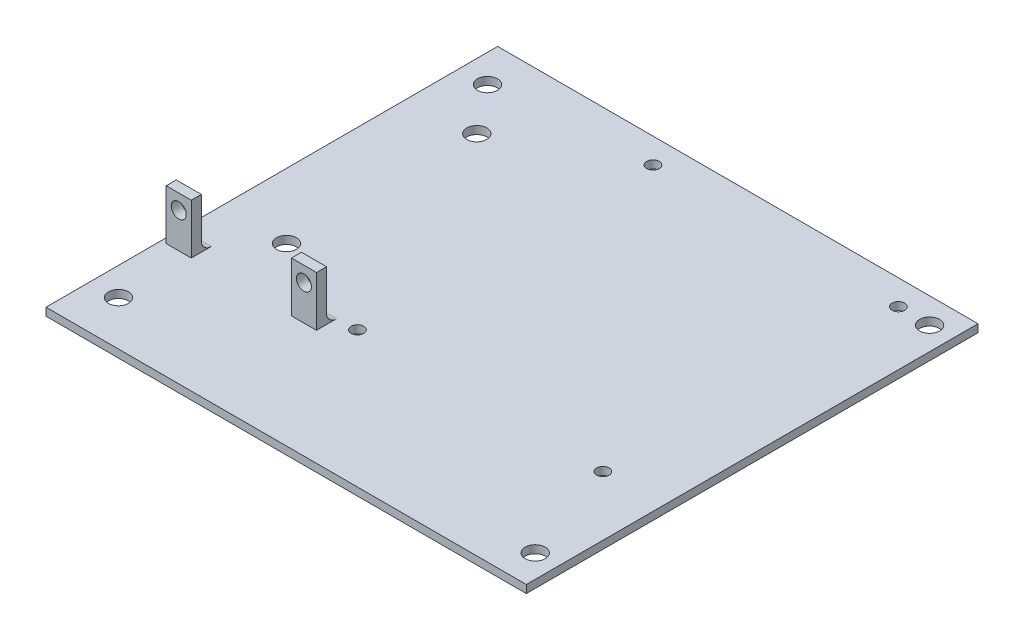
SolidWorks part; units mm, degrees
other "DetailItem3"
material "ABS"
ref_plane "Front Plane" through (0, 0, 0) normal (0, 0, 1) x (1, 0, 0)
ref_plane "Top Plane" through (0, 0, 0) normal (0, 1, 0) x (1, 0, 0)
ref_plane "Right Plane" through (0, 0, 0) normal (1, 0, 0) x (0, 0, -1)
sketch "Sketch1" plane through (0, 0, 0) normal (0, 1, 0) x (1, 0, 0)
  line L1 (-32.2441, 108.719) -> (64.6459, 108.719)
  line L2 (-32.2441, 108.719) -> (-32.2441, 18.549)
  line L3 (-32.2441, 18.549) -> (64.6459, 18.549)
  line L4 (64.6459, 108.719) -> (64.6459, 18.549)
  dimension "D1" = 96.89
  dimension "D2" = 90.17
extrude "PCB" add sketch "Sketch1" along normal blind 1.57
sketch "Sketch2" plane through (0, 1.57, 0) normal (0, 1, 0) x (1, 0, 0)
  line L0 (64.6459, 18.549) -> (64.6459, 108.719) construction
  line L1 (-32.2441, 18.549) -> (64.6459, 18.549) construction
  circle A0 centre (59.5659, 24.899) radius 2
  circle A1 centre (-26.1641, 27.439) radius 2
  circle A2 centre (-26.1641, 101.099) radius 2
  circle A3 centre (59.5659, 103.639) radius 2
  dimension "D3" = 4
  dimension "D6" = 4
  dimension "D11" = 4
  dimension "D12" = 4
  dimension "D1" = 5.08
  dimension "D2" = 6.35
  dimension "D4" = 90.81
  dimension "D5" = 8.89
  dimension "D7" = 90.81
  dimension "D8" = 5.08
  dimension "D9" = 85.09
  dimension "D10" = 82.55
extrude "M3 Mounting Holes" cut sketch "Sketch2" against normal blind 1.57
sketch "Sketch5" plane through (0, 1.57, 0) normal (0, 1, 0) x (1, 0, 0)
  line L0 (64.6459, 108.719) -> (-32.2441, 108.719) construction
  line L1 (-32.2441, 18.549) -> (-31.7441, 18.549)
  line L2 (-32.2441, 18.549) -> (-32.2441, 108.719)
  line L3 (-32.2441, 108.719) -> (-31.7441, 108.719)
  line L4 (-31.7441, 18.549) -> (-31.7441, 108.719)
  line L5 (-32.2441, 18.549) -> (64.6459, 18.549) construction
  line L6 (64.6459, 108.719) -> (64.1459, 108.719)
  line L7 (64.6459, 108.719) -> (64.6459, 18.549)
  line L8 (64.6459, 18.549) -> (64.1459, 18.549)
  line L9 (64.1459, 108.719) -> (64.1459, 18.549)
  dimension "D1" = 0.5
  dimension "D2" = 0.5
extrude "Cut-Extrude1" cut sketch "Sketch5" against normal through all
sketch "Sketch8" plane through (0, 1.57, 0) normal (0, 1, 0) x (1, 0, 0)
  line L1 (-31.7441, 18.549) -> (-31.7441, 108.719) construction
  line L3 (64.1459, 108.719) -> (-31.7441, 108.719) construction
  circle A0 centre (3.2559, 45.719) radius 1.25
  circle A1 centre (52.2559, 45.719) radius 1.25
  circle A2 centre (4.2559, 103.719) radius 1.25
  circle A3 centre (53.2559, 103.719) radius 1.25
  dimension "D1" = 2.5
  dimension "D3" = 2.5
  dimension "D5" = 2.5
  dimension "D6" = 2.5
  dimension "D2" = 5
  dimension "D4" = 63
  dimension "D7" = 58
  dimension "D8" = 58
  dimension "D9" = 49
  dimension "D10" = 35
  dimension "D11" = 36
  dimension "D12" = 49
extrude "RPi mounting hole" cut sketch "Sketch8" against normal blind 10
sketch "Sketch9" plane through (0, 1.57, 0) normal (0, 1, 0) x (1, 0, 0)
  line L0 (-31.7441, 18.549) -> (64.1459, 18.549) construction
  line L1 (-31.7441, 18.549) -> (-31.7441, 108.719) construction
  circle A0 centre (-18.7441, 91.549) radius 2
  circle A1 centre (-18.7441, 53.549) radius 2
  dimension "D1" = 4
  dimension "D2" = 4
  dimension "D3" = 38
  dimension "D4" = 35
  dimension "D5" = 13
  dimension "D6" = 13
extrude "PowerAdapterHoles" cut sketch "Sketch9" against normal blind 10
sketch "Sketch10" plane through (0, 1.57, 0) normal (0, 1, 0) x (1, 0, 0)
  line L0 (-31.7441, 18.549) -> (64.1459, 18.549) construction
  line L1 (-30.7441, 41.549) -> (-25.7441, 41.549)
  line L2 (-30.7441, 41.549) -> (-30.7441, 43.549)
  line L3 (-30.7441, 43.549) -> (-25.7441, 43.549)
  line L4 (-25.7441, 41.549) -> (-25.7441, 43.549)
  line L5 (-0.7441, 41.549) -> (-5.7441, 41.549)
  line L6 (-0.7441, 41.549) -> (-0.7441, 43.549)
  line L7 (-0.7441, 43.549) -> (-5.7441, 43.549)
  line L8 (-5.7441, 41.549) -> (-5.7441, 43.549)
  line L9 (-31.7441, 18.549) -> (-31.7441, 108.719) construction
  dimension "D1" = 2
  dimension "D2" = 2
  dimension "D3" = 5
  dimension "D4" = 5
  dimension "D5" = 20
  dimension "D6" = 23
  dimension "D7" = 23
  dimension "D8" = 1
extrude "DSub Holder" add sketch "Sketch10" along normal blind 10
fillet "Fillet2" radius 2 2 edges at (-28.2441, 1.57, -43.549) (-3.2441, 1.57, -43.549)
sketch "Sketch11" plane through (0, 0, -41.549) normal (0, 0, 1) x (1, 0, 0)
  line L2 (-30.7441, 1.57) -> (-25.7441, 1.57) construction
  line L3 (-5.7441, 1.57) -> (-0.7441, 1.57) construction
  line L4 (-30.7441, 11.57) -> (-30.7441, 1.57) construction
  circle A0 centre (-28.2441, 8.57) radius 1.5
  circle A1 centre (-3.2541, 8.57) radius 1.5
  dimension "D1" = 3
  dimension "D2" = 3
  dimension "D3" = 24.99
  dimension "D4" = 7
  dimension "D5" = 7
  dimension "D6" = 2.5
extrude "DSub Fields" cut sketch "Sketch11" against normal up to next
